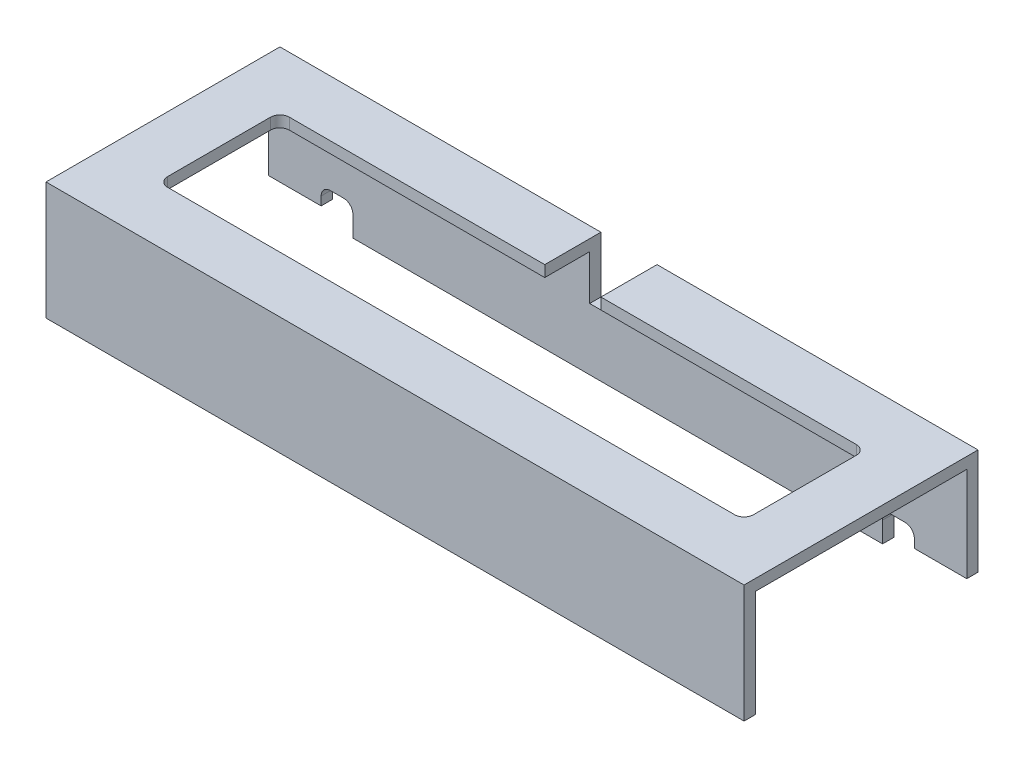
SolidWorks part; units mm, degrees
material "aluminio"
ref_plane "Alzado" through (0, 0, 0) normal (0, 0, 1) x (1, 0, 0)
ref_plane "Planta" through (0, 0, 0) normal (0, 1, 0) x (1, 0, 0)
ref_plane "Vista lateral" through (0, 0, 0) normal (1, 0, 0) x (0, 0, -1)
sketch "Sketch1" plane through (0, 0, 0) normal (1, 0, 0) x (0, 0, -1)
  line L0 (0, 0) -> (6, 0)
  line L1 (6, 0) -> (6, 57)
  line L2 (6, 57) -> (119, 57)
  line L3 (119, 57) -> (119, 0)
  line L4 (119, 0) -> (125, 0)
  line L5 (125, 0) -> (125, 63)
  line L6 (125, 63) -> (0, 63)
  line L7 (0, 63) -> (0, 0)
  dimension "D1" = 125
  dimension "D2" = 6
  dimension "D3" = 6
  dimension "D4" = 6
  dimension "D6" = 63
extrude "Boss-Extrude1" add sketch "Sketch1" along normal up to surface (311.5 mm away) and the other way up to surface (61.5 mm away)
sketch "Sketch2" plane through (0, 0, -125) normal (0, 0, -1) x (-1, 0, 0)
  line L1 (-280.5, 6.4) -> (-322.5, 6.4) construction
  line L2 (16.5, 0) -> (16.5, 16)
  line L3 (-283.5, 6.4) -> (-322.5, 6.4) construction
  line L4 (61.5, 63) -> (-311.5, 63)
  line L5 (-311.5, 63) -> (-311.5, 0)
  line L6 (-311.5, 0) -> (61.5, 0)
  line L7 (61.5, 0) -> (61.5, 63)
  line L8 (61.5, 63) -> (-311.5, 63)
  line L9 (-311.5, 63) -> (-311.5, 0)
  line L10 (-311.5, 0) -> (61.5, 0) construction
  line L11 (61.5, 0) -> (61.5, 63)
  line L12 (-125, 0) -> (-125, 63) construction
  line L13 (-311.5, 0) -> (61.5, 0)
  line L14 (16.5, 16) -> (33.5, 16)
  line L15 (-283.5, 6.4) -> (-311.5, 6.4)
  line L16 (-311.5, 0) -> (-311.5, 6.4)
  line L17 (33.5, 6.4) -> (33.5, 16)
  line L18 (-110, 33) -> (-140, 33)
  line L19 (-110, 33) -> (-110, 63)
  line L20 (-110, 63) -> (-140, 63)
  line L21 (-140, 33) -> (-140, 63)
  line L22 (-110, 33) -> (-140, 63) construction
  line L23 (-110, 63) -> (-140, 33) construction
  line L24 (33.5, 6.4) -> (61.5, 6.4)
  line L25 (61.5, 0) -> (-311.5, 0)
  line L27 (-266.5, 0) -> (-266.5, 16)
  line L28 (-266.5, 16) -> (-283.5, 16)
  line L29 (-311.5, 0) -> (61.5, 0)
  line L30 (-311.5, 57) -> (-311.5, 0)
  line L31 (61.5, 57) -> (-311.5, 57)
  line L32 (61.5, 0) -> (61.5, 57)
  line L34 (-311.5, 57) -> (-311.5, 0)
  line L35 (61.5, 57) -> (-311.5, 57)
  line L36 (61.5, 0) -> (61.5, 57)
  line L37 (-283.5, 6.4) -> (-283.5, 16)
  circle A1 centre (-277.52, 10.9) radius 4.34 construction
  circle A3 centre (-277.52, 10.9) radius 4.34
  point P14 (-125, 48)
  line M1 (61.5, 0) -> (61.5, 63)
  line M4 (-311.5, 0) -> (61.5, 0)
  dimension "D6" = 16
  dimension "D1" = 0
  dimension "D2" = 45
  dimension "D3" = 30
  dimension "D4" = 30
  dimension "D7" = 28
  dimension "D5" = 0
extrude "Cortar-Extruir1" cut sketch "Sketch2" against normal blind 30 contours L37 L15 L9 L27 L28 A3 M4 | A3 | L19 L35 L21 L18 | L35 L19 L8 L21 | L24 L17 L14 L2 M4 M1
sketch "Croquis1" plane through (0, 63, 0) normal (0, 1, 0) x (1, 0, 0)
  line L0 (-31.5, 30) -> (281.5, 30)
  line L1 (281.5, 30) -> (281.5, 95)
  line L2 (281.5, 95) -> (170, 95)
  line L6 (80, 95) -> (-31.5, 95)
  line L7 (-31.5, 95) -> (-31.5, 30)
  line L8 (140, 95) -> (110, 95)
  line L9 (110, 95) -> (110, 125)
  line L10 (110, 125) -> (-61.5, 125)
  line L11 (-61.5, 125) -> (-61.5, 0)
  line L12 (-61.5, 0) -> (311.5, 0)
  line L13 (311.5, 0) -> (311.5, 125)
  line L14 (311.5, 125) -> (140, 125)
  line L15 (140, 125) -> (140, 95)
  line L16 (140, 95) -> (110, 95)
  line L17 (110, 95) -> (110, 125)
  line L18 (110, 125) -> (-61.5, 125)
  line L19 (-61.5, 125) -> (-61.5, 0) construction
  line L20 (-61.5, 0) -> (311.5, 0) construction
  line L21 (311.5, 0) -> (311.5, 125)
  line L22 (311.5, 125) -> (140, 125)
  line L23 (140, 125) -> (140, 95)
  line L24 (80, 95) -> (170, 95)
  line L32 (170, 95) -> (170, 65) construction
  line L33 (80, 65) -> (80, 95) construction
  line L34 (170, 65) -> (80, 65) construction
  dimension "D1" = 0
  dimension "D2" = 30
extrude "Cortar-Extruir3" cut sketch "Croquis1" against normal up to next
fillet "Redondeo1" radius 5 8 edges at (-33.5, 16, -122) (-16.5, 16, -122) (266.5, 16, -122) (283.5, 16, -122) (281.5, 60, -30) (281.5, 60, -95) (-31.5, 60, -30) (-31.5, 60, -95)
